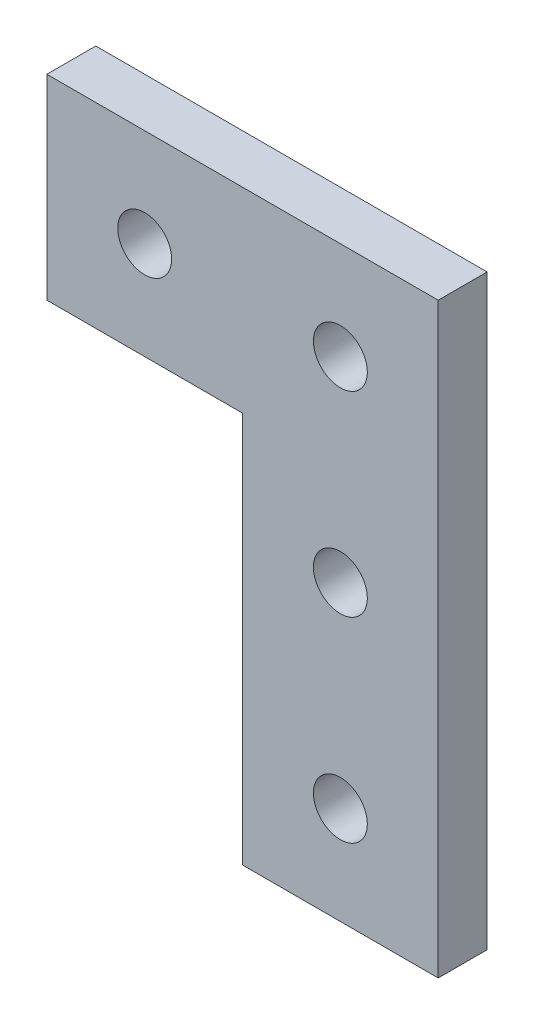
SolidWorks part; units mm, degrees
ref_plane "Front Plane" through (0, 0, 0) normal (0, 0, 1) x (1, 0, 0)
ref_plane "Top Plane" through (0, 0, 0) normal (0, 1, 0) x (1, 0, 0)
ref_plane "Right Plane" through (0, 0, 0) normal (1, 0, 0) x (0, 0, -1)
sketch "Sketch1" plane through (0, 0, 0) normal (0, 0, 1) x (1, 0, 0)
  line L0 (12.7, 0) -> (-12.7, 0)
  line L1 (-12.7, 0) -> (-12.7, 50.8)
  line L7 (12.7, 50.8) -> (12.7, 0)
  line L8 (12.7, 50.8) -> (12.7, 76.2)
  line L10 (-63.1, 76.2) -> (-63.1, 50.8)
  line L12 (12.7, 76.2) -> (-63.1, 76.2)
  line L13 (-63.1, 50.8) -> (-12.7, 50.8)
  dimension "D1" = 25.4
  dimension "D2" = 12.7
  dimension "D3" = 50.8
  dimension "D4" = 50.4
  dimension "D5" = 25.4
extrude "Boss-Extrude1" add sketch "Sketch1" along normal blind 6.35
sketch "Sketch2" plane through (0, 0, 6.35) normal (0, 0, 1) x (1, 0, 0)
  line L0 (0, 0) -> (0, 67) construction
  line L2 (-28.9, 63.5) -> (-21.9, 63.5) construction
  line L5 (-12.7, 0) -> (12.7, 0) construction
  line L6 (-3.5, 63.5) -> (3.5, 63.5) construction
  line L7 (0, 63.5) -> (-63.1, 63.5) construction
  line L8 (-63.1, 76.2) -> (-63.1, 50.8) construction
  circle A0 centre (0, 63.5) radius 3.5
  circle A2 centre (-25.4, 63.5) radius 3.5
  circle A3 centre (0, 38.1) radius 3.5
  circle A4 centre (0, 12.7) radius 3.5
  circle A5 centre (-50.8, 63.5) radius 3.5
  dimension "D1" = 7
  dimension "D2" = 7
  dimension "D3" = 7
  dimension "D4" = 7
  dimension "D5" = 7
  dimension "D6" = 12.7
  dimension "D7" = 25.4
  dimension "D8" = 25.4
  dimension "D9" = 25.4
extrude "Cut-Extrude1" cut sketch "Sketch2" against normal through all
sketch "Sketch3" plane through (-63.1, 0, 0) normal (-1, 0, 0) x (0, 0, 1)
  line L1 (-3.5444, 82.2439) -> (10.6872, 82.2439)
  line L2 (-3.5444, 82.2439) -> (-3.5444, 47.7323)
  line L3 (-3.5444, 47.7323) -> (10.6872, 47.7323)
  line L4 (10.6872, 82.2439) -> (10.6872, 47.7323)
  line L5 (-3.5444, 82.2439) -> (10.6872, 47.7323) construction
  line L6 (-3.5444, 47.7323) -> (10.6872, 82.2439) construction
  point P0 (3.5714, 64.9881)
extrude "Cut-Extrude2" cut sketch "Sketch3" against normal blind 25
